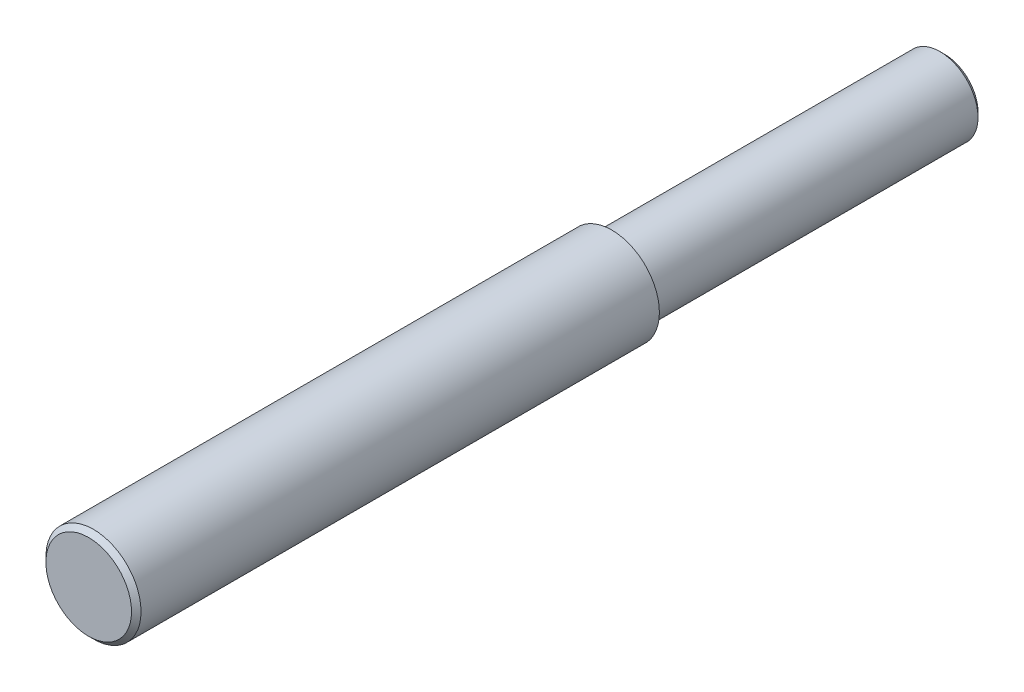
SolidWorks part; units mm, degrees
material "1.4462 (X2CrNiMoN22-5-3)"
ref_plane "Front Plane" through (0, 0, 0) normal (0, 0, 1) x (1, 0, 0)
ref_plane "Top Plane" through (0, 0, 0) normal (0, 1, 0) x (1, 0, 0)
ref_plane "Right Plane" through (0, 0, 0) normal (1, 0, 0) x (0, 0, -1)
sketch "Sketch1" plane through (0, 0, 0) normal (0, 0, 1) x (1, 0, 0)
  circle A0 centre (0, 0) radius 1
  dimension "D1" = 2
extrude "Boss-Extrude1" add sketch "Sketch1" against normal blind 18
sketch "Sketch2" plane through (0, 0, -18) normal (0, 0, -1) x (-1, 0, 0)
  circle A0 centre (0, 0) radius 0.8
  dimension "D1" = 1.6
extrude "Cut-Extrude1" cut sketch "Sketch2" against normal blind 7 flip side to cut
chamfer "Chamfer1" distance 0.1 angle 45 1 edges at (-0.8, 0, -18)
chamfer "Chamfer2" distance 0.1 angle 45 1 edges at (1, 0, 0)
